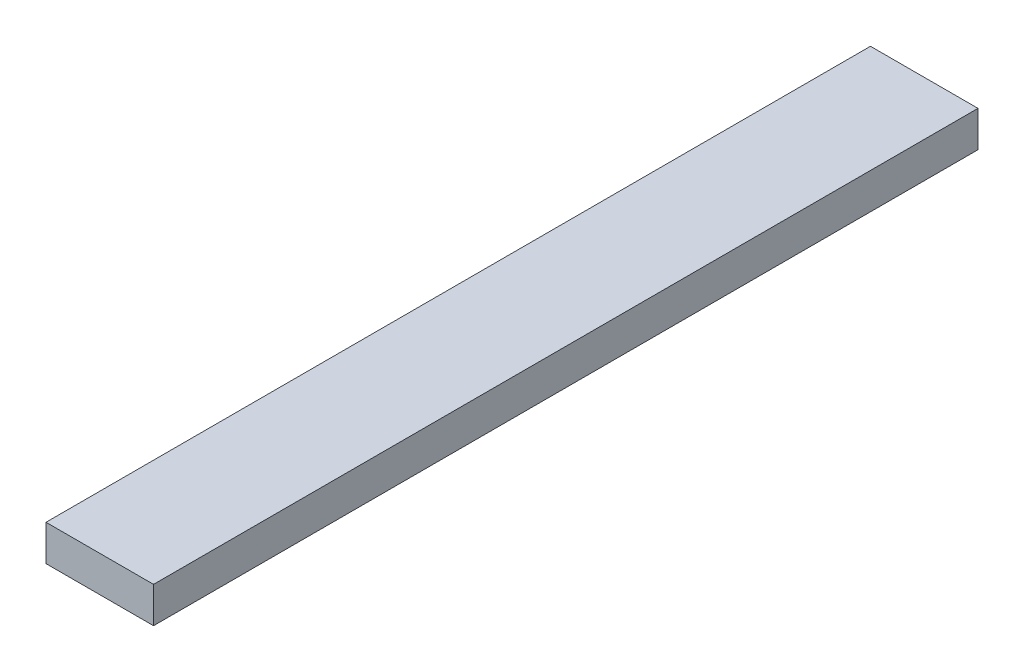
SolidWorks part; units mm, degrees
ref_plane "Front Plane" through (0, 0, 0) normal (0, 0, 1) x (1, 0, 0)
ref_plane "Top Plane" through (0, 0, 0) normal (0, 1, 0) x (1, 0, 0)
ref_plane "Right Plane" through (0, 0, 0) normal (1, 0, 0) x (0, 0, -1)
sketch "Sketch1" plane through (0, 0, 0) normal (0, 0, 1) x (1, 0, 0)
  line L1 (-30, -10) -> (30, -10)
  line L2 (-30, -10) -> (-30, 10)
  line L3 (-30, 10) -> (30, 10)
  line L4 (30, -10) -> (30, 10)
  line L5 (-30, -10) -> (30, 10) construction
  line L6 (-30, 10) -> (30, -10) construction
  point P0 (0, 0)
  dimension "D1" = 20
  dimension "D2" = 60
extrude "Boss-Extrude1" add sketch "Sketch1" along normal mid plane 460
